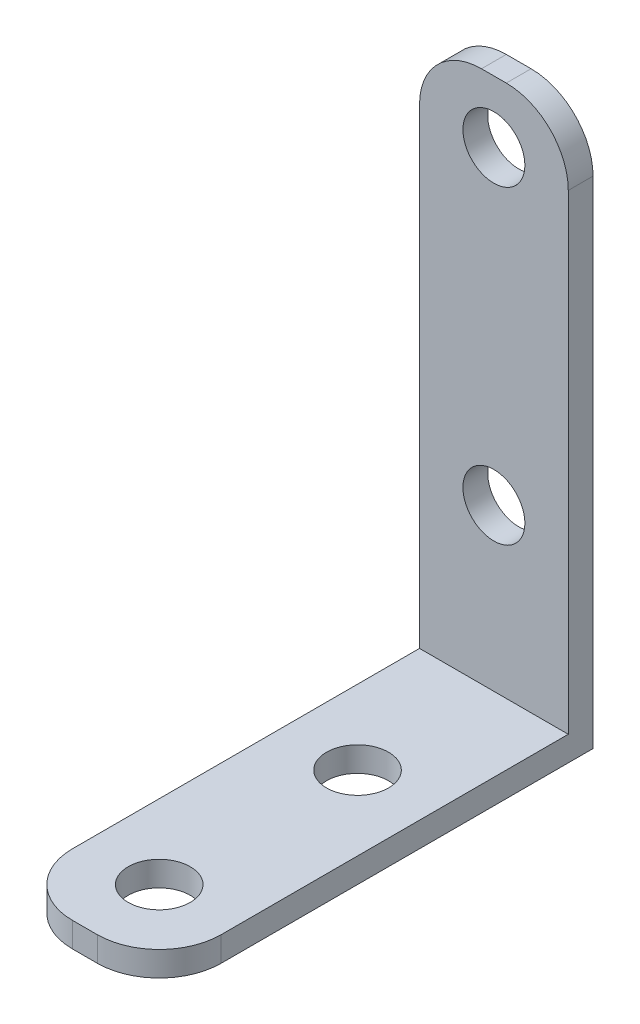
SolidWorks part; units mm, degrees
ref_plane "Front Plane" through (0, 0, 0) normal (0, 0, 1) x (1, 0, 0)
ref_plane "Top Plane" through (0, 0, 0) normal (0, 1, 0) x (1, 0, 0)
ref_plane "Right Plane" through (0, 0, 0) normal (1, 0, 0) x (0, 0, -1)
sketch "Sketch1" plane through (0, 0, 0) normal (0, 0, 1) x (1, 0, 0)
  line L1 (6, -22.5) -> (-6, -22.5)
  line L2 (6, -22.5) -> (6, 22.5)
  line L3 (6, 22.5) -> (-6, 22.5)
  line L4 (-6, -22.5) -> (-6, 22.5)
  line L5 (6, -22.5) -> (-6, 22.5) construction
  line L6 (6, 22.5) -> (-6, -22.5) construction
  circle A0 centre (0, -7.5) radius 2.5
  circle A1 centre (0, 17.5) radius 2.5
  point P0 (0, 0)
  dimension "D3" = 5
  dimension "D4" = 5
  dimension "D1" = 45
  dimension "D2" = 12
  dimension "D5" = 15
  dimension "25" = 25
extrude "Boss-Extrude1" add sketch "Sketch1" along normal blind 2
fillet "Fillet3" radius 5 2 edges at (6, 22.5, 1) (-6, 22.5, 1)
sketch "Sketch2" plane through (0, 0, 2) normal (0, 0, 1) x (1, 0, 0)
  line L0 (-6, -22.5) -> (6, -22.5) construction
  line L1 (-6, -22.5) -> (6, -22.5)
  line L2 (-6, -22.5) -> (-6, -20.5)
  line L3 (-6, 17.5) -> (-6, -22.5) construction
  line L4 (-6, -20.5) -> (6, -20.5)
  line L5 (6, -22.5) -> (6, 17.5) construction
  line L6 (6, -20.5) -> (6, -22.5)
  dimension "D1" = 2
extrude "Boss-Extrude2" add sketch "Sketch2" along normal blind 33
sketch "Sketch3" plane through (0, -20.5, 0) normal (0, 1, 0) x (1, 0, 0)
  line L1 (-1, 0) -> (-6, 0) construction
  circle A0 centre (0, -13) radius 2.5
  circle A1 centre (0, -29) radius 2.5
  dimension "D1" = 5
  dimension "D2" = 13
  dimension "D3" = 16
extrude "Cut-Extrude1" cut sketch "Sketch3" against normal blind 33
fillet "Fillet4" radius 5 2 edges at (-6, -21.5, 35) (6, -21.5, 35)
